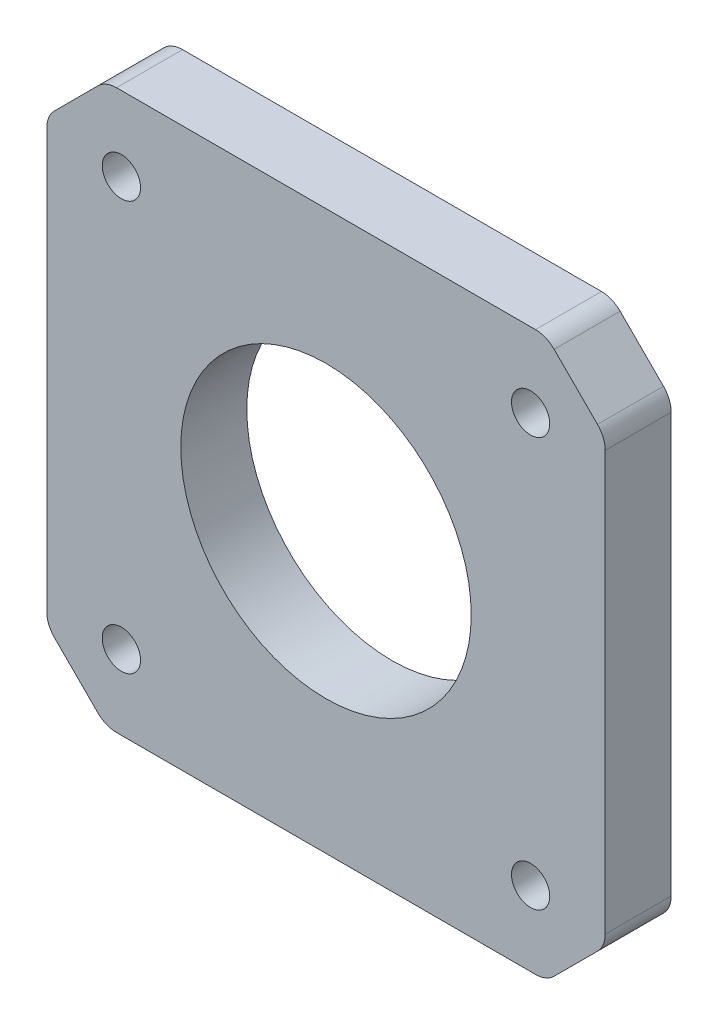
SolidWorks part; units mm, degrees
ref_plane "Front Plane" through (0, 0, 0) normal (0, 0, 1) x (1, 0, 0)
ref_plane "Top Plane" through (0, 0, 0) normal (0, 1, 0) x (1, 0, 0)
ref_plane "Right Plane" through (0, 0, 0) normal (1, 0, 0) x (0, 0, -1)
sketch "Sketch1" plane through (0, 0, 0) normal (0, 0, 1) x (1, 0, 0)
  line L0 (-15.5, 15.5) -> (-15.5, -17.8129) construction
  line L1 (15.5, -15.5) -> (-26.9904, -15.5) construction
  line L8 (-20.5642, -17.2814) -> (-17.2814, -20.5642)
  line L9 (-15.8672, -21.15) -> (15.8672, -21.15)
  line L10 (17.2814, -20.5642) -> (20.5642, -17.2814)
  line L11 (21.15, -15.8672) -> (21.15, 15.8672)
  line L12 (20.5642, 17.2814) -> (17.2814, 20.5642)
  line L13 (15.8672, 21.15) -> (-15.8672, 21.15)
  line L14 (-17.2814, 20.5642) -> (-20.5642, 17.2814)
  line L15 (-21.15, 15.8672) -> (-21.15, -15.8672)
  line L16 (-20.5642, -17.2814) -> (-17.2814, -20.5642)
  line L17 (-15.8672, -21.15) -> (15.8672, -21.15)
  line L18 (17.2814, -20.5642) -> (20.5642, -17.2814)
  line L19 (21.15, -15.8672) -> (21.15, 15.8672)
  line L20 (20.5642, 17.2814) -> (17.2814, 20.5642)
  line L21 (15.8672, 21.15) -> (-15.8672, 21.15)
  line L22 (-17.2814, 20.5642) -> (-20.5642, 17.2814)
  line L23 (-21.15, 15.8672) -> (-21.15, -15.8672)
  circle A0 centre (-15.5, 15.5) radius 1.45
  circle A1 centre (15.5, 15.5) radius 1.45
  circle A2 centre (15.5, -15.5) radius 1.45
  circle A3 centre (-15.5, -15.5) radius 1.45
  circle A4 centre (0, 0) radius 11 construction
  circle A5 centre (0, 0) radius 11
  arc A8 (-17.2814, -20.5642) -> (-15.8672, -21.15) centre (-15.8672, -19.15) ccw
  arc A9 (15.8672, -21.15) -> (17.2814, -20.5642) centre (15.8672, -19.15) ccw
  arc A10 (20.5642, -17.2814) -> (21.15, -15.8672) centre (19.15, -15.8672) ccw
  arc A11 (21.15, 15.8672) -> (20.5642, 17.2814) centre (19.15, 15.8672) ccw
  arc A12 (17.2814, 20.5642) -> (15.8672, 21.15) centre (15.8672, 19.15) ccw
  arc A13 (-15.8672, 21.15) -> (-17.2814, 20.5642) centre (-15.8672, 19.15) ccw
  arc A14 (-20.5642, 17.2814) -> (-21.15, 15.8672) centre (-19.15, 15.8672) ccw
  arc A15 (-21.15, -15.8672) -> (-20.5642, -17.2814) centre (-19.15, -15.8672) ccw
  arc A16 (-17.2814, -20.5642) -> (-15.8672, -21.15) centre (-15.8672, -19.15) ccw
  arc A17 (15.8672, -21.15) -> (17.2814, -20.5642) centre (15.8672, -19.15) ccw
  arc A18 (20.5642, -17.2814) -> (21.15, -15.8672) centre (19.15, -15.8672) ccw
  arc A19 (21.15, 15.8672) -> (20.5642, 17.2814) centre (19.15, 15.8672) ccw
  arc A20 (17.2814, 20.5642) -> (15.8672, 21.15) centre (15.8672, 19.15) ccw
  arc A21 (-15.8672, 21.15) -> (-17.2814, 20.5642) centre (-15.8672, 19.15) ccw
  arc A22 (-20.5642, 17.2814) -> (-21.15, 15.8672) centre (-19.15, 15.8672) ccw
  arc A23 (-21.15, -15.8672) -> (-20.5642, -17.2814) centre (-19.15, -15.8672) ccw
  dimension "D2" = 2.9
  dimension "D1" = 0
extrude "Boss-Extrude1" add sketch "Sketch1" along normal blind 5 contours L19 A19 L20 A20 L21 A21 L22 A22 L23 A23 L16 A16 L17 A17 L18 A18
